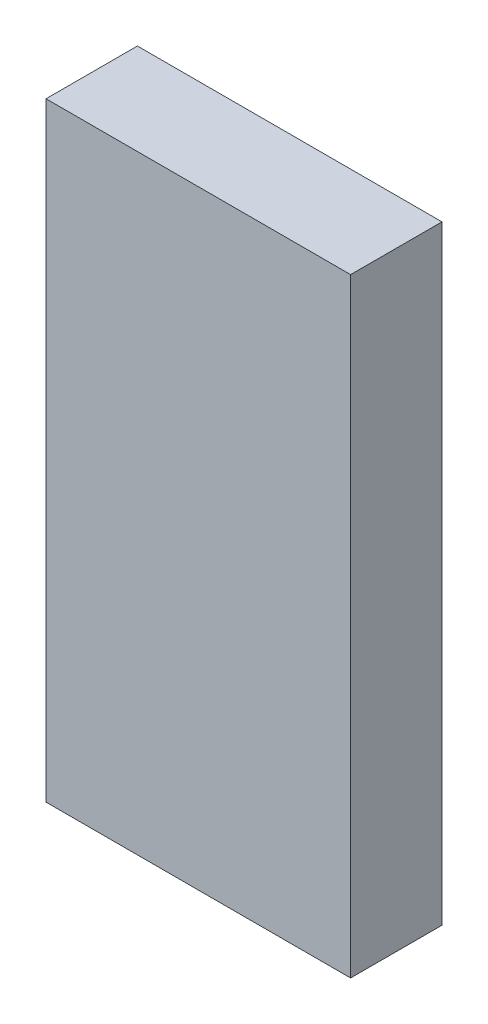
SolidWorks part; units mm, degrees
ref_plane "Front Plane" through (0, 0, 0) normal (0, 0, 1) x (1, 0, 0)
ref_plane "Top Plane" through (0, 0, 0) normal (0, 1, 0) x (1, 0, 0)
ref_plane "Right Plane" through (0, 0, 0) normal (1, 0, 0) x (0, 0, -1)
sketch "Sketch1" plane through (0, 0, 0) normal (0, 0, 1) x (1, 0, 0)
  line L1 (-12.7, -25.4) -> (12.7, -25.4)
  line L2 (-12.7, -25.4) -> (-12.7, 25.4)
  line L3 (-12.7, 25.4) -> (12.7, 25.4)
  line L4 (12.7, -25.4) -> (12.7, 25.4)
  line L5 (-12.7, -25.4) -> (12.7, 25.4) construction
  line L6 (-12.7, 25.4) -> (12.7, -25.4) construction
  point P0 (0, 0)
  dimension "D1" = 50.8
  dimension "D2" = 25.4
extrude "Boss-Extrude1" add sketch "Sketch1" along normal blind 7.62
